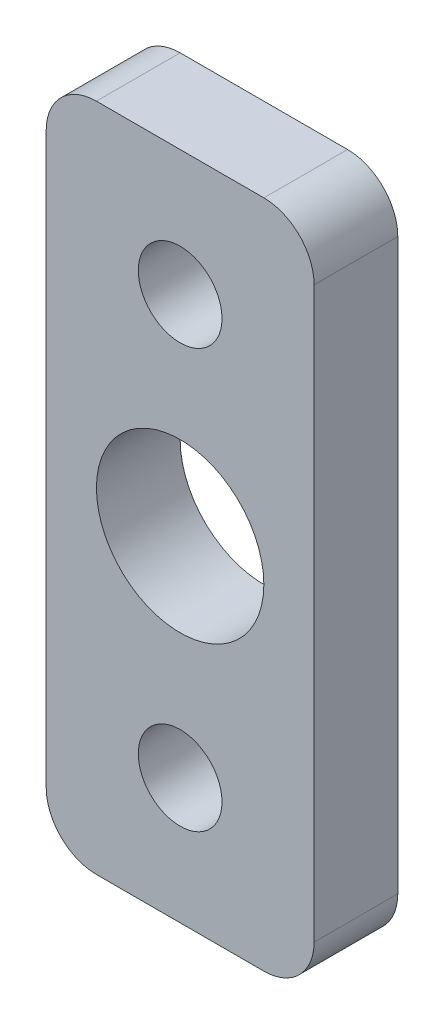
SolidWorks part; units mm, degrees
material "瞎编数据的PLA"
ref_plane "前视基准面" through (0, 0, 0) normal (0, 0, 1) x (1, 0, 0)
ref_plane "上视基准面" through (0, 0, 0) normal (0, 1, 0) x (1, 0, 0)
ref_plane "右视基准面" through (0, 0, 0) normal (1, 0, 0) x (0, 0, -1)
sketch "草图1" plane through (0, 0, 0) normal (0, 0, 1) x (1, 0, 0)
  line L0 (0, 0) -> (0, 25) construction
  line L2 (-8, 32.5) -> (8, 32.5)
  line L3 (-8, 32.5) -> (-8, -7.5)
  line L4 (-8, -7.5) -> (8, -7.5)
  line L5 (8, 32.5) -> (8, -7.5)
  line L6 (-8, 32.5) -> (8, -7.5) construction
  line L7 (-8, -7.5) -> (8, 32.5) construction
  circle A0 centre (0, 25) radius 2.5
  circle A1 centre (0, 0) radius 2.5
  circle A2 centre (0, 12.5) radius 5
  point P5 (0, 12.5)
  dimension "D1" = 5
  dimension "D5" = 10
  dimension "D2" = 25
  dimension "D3" = 16
  dimension "D4" = 40
extrude "凸台-拉伸1" add sketch "草图1" along normal blind 5
fillet "圆角1" radius 3 4 edges at (8, 32.5, 2.5) (-8, 32.5, 2.5) (-8, -7.5, 2.5) (8, -7.5, 2.5)
